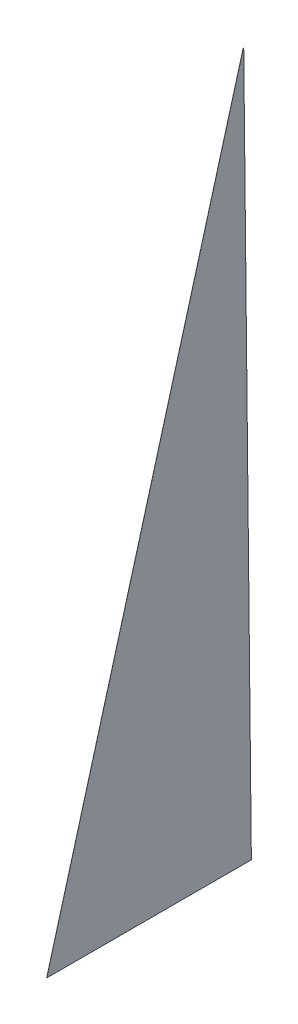
SolidWorks part; units mm, degrees
material "Corrugated Paper"
ref_plane "Front Plane" through (0, 0, 0) normal (0, 0, 1) x (1, 0, 0)
ref_plane "Top Plane" through (0, 0, 0) normal (0, 1, 0) x (1, 0, 0)
ref_plane "Right Plane" through (0, 0, 0) normal (1, 0, 0) x (0, 0, -1)
sketch "Sketch1" plane through (0, 0, 0) normal (1, 0, 0) x (0, 0, -1)
  line L0 (0, 0) -> (168.45, 605.88)
  line L1 (168.45, 605.88) -> (175, 0)
  line L2 (175, 0) -> (0, 0)
  dimension "D1" = 175
  dimension "D2" = 605.88
  dimension "D3" = 168.45
extrude "Boss-Extrude1" add sketch "Sketch1" along normal blind 0.064
